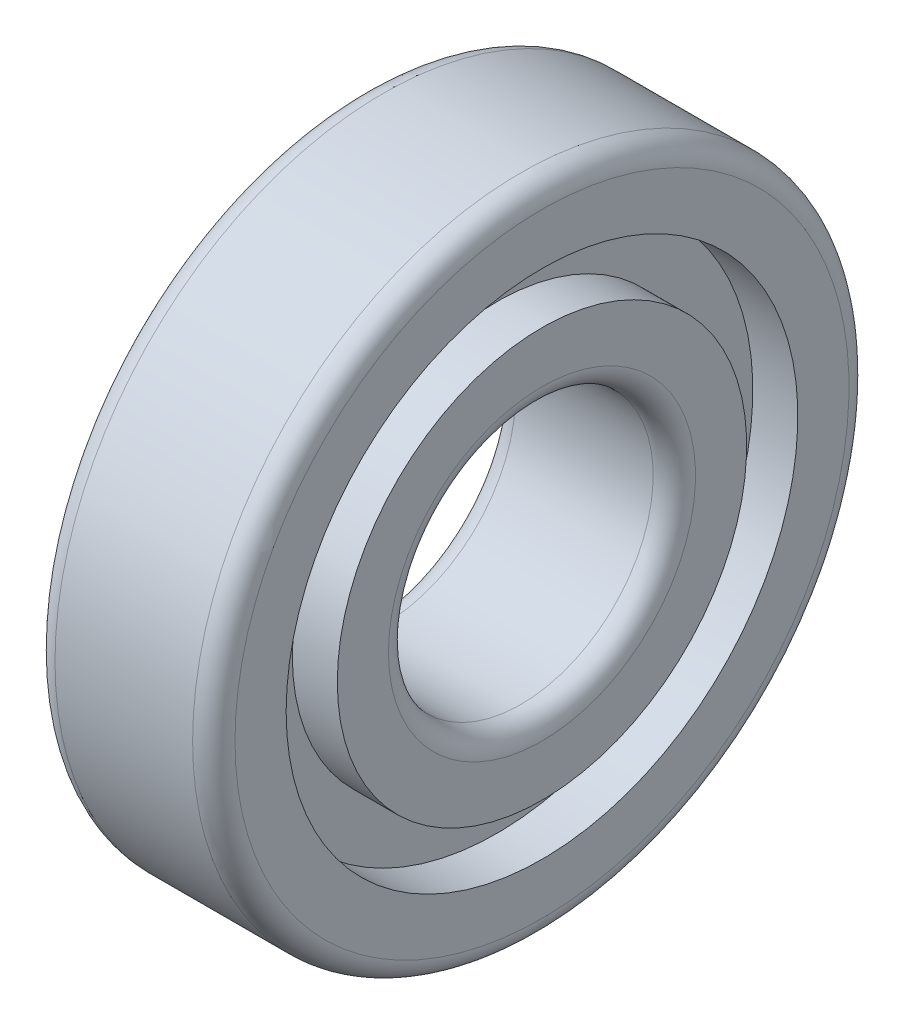
SolidWorks part; units mm, degrees
ref_plane "Спереди" through (0, 0, 0) normal (0, 0, 1) x (1, 0, 0)
ref_plane "Сверху" through (0, 0, 0) normal (0, 1, 0) x (1, 0, 0)
ref_plane "Справа" through (0, 0, 0) normal (1, 0, 0) x (0, 0, -1)
sketch "Эскиз1" plane through (0, 0, 0) normal (0, 0, 1) x (1, 0, 0)
  line L0 (6.5, 12.5) -> (-6.5, 12.5)
  line L1 (-8.5, 14.5) -> (-8.5, 19.3333)
  line L2 (-8.5, 19.3333) -> (-4.25, 19.3333)
  line L3 (-4.25, 19.3333) -> (-4.25, 24.1667)
  line L4 (-4.25, 24.1667) -> (-8.5, 24.1667)
  line L5 (-8.5, 24.1667) -> (-8.5, 29)
  line L6 (-6.5, 31) -> (6.5, 31)
  line L7 (-873.9917, 0) -> (42825.5954, 0) construction
  line L8 (0, -873.9917) -> (0, 42825.5954) construction
  line L9 (8.5, 24.1667) -> (8.5, 29)
  line L10 (4.25, 24.1667) -> (8.5, 24.1667)
  line L11 (4.25, 19.3333) -> (4.25, 24.1667)
  line L12 (8.5, 19.3333) -> (4.25, 19.3333)
  line L13 (8.5, 14.5) -> (8.5, 19.3333)
  arc A0 (-6.5, 12.5) -> (-8.5, 14.5) centre (-6.5, 14.5) cw
  arc A1 (-8.5, 29) -> (-6.5, 31) centre (-6.5, 29) cw
  arc A2 (8.5, 29) -> (6.5, 31) centre (6.5, 29) ccw
  arc A3 (6.5, 12.5) -> (8.5, 14.5) centre (6.5, 14.5) ccw
  point P12 (0, 0)
  point P14 (0, 0)
  point P25 (0, 31)
  point P29 (0, 12.5)
  dimension "D3" = 2
  dimension "B" = 17
  dimension "D1" = 25
  dimension "D2" = 62
  dimension "D4" = 4.25
revolve "Повернуть1" add sketch "Эскиз1" angle 360 about L7
equation "\"D4@Эскиз1\"=\"B@Эскиз1\"/4"
